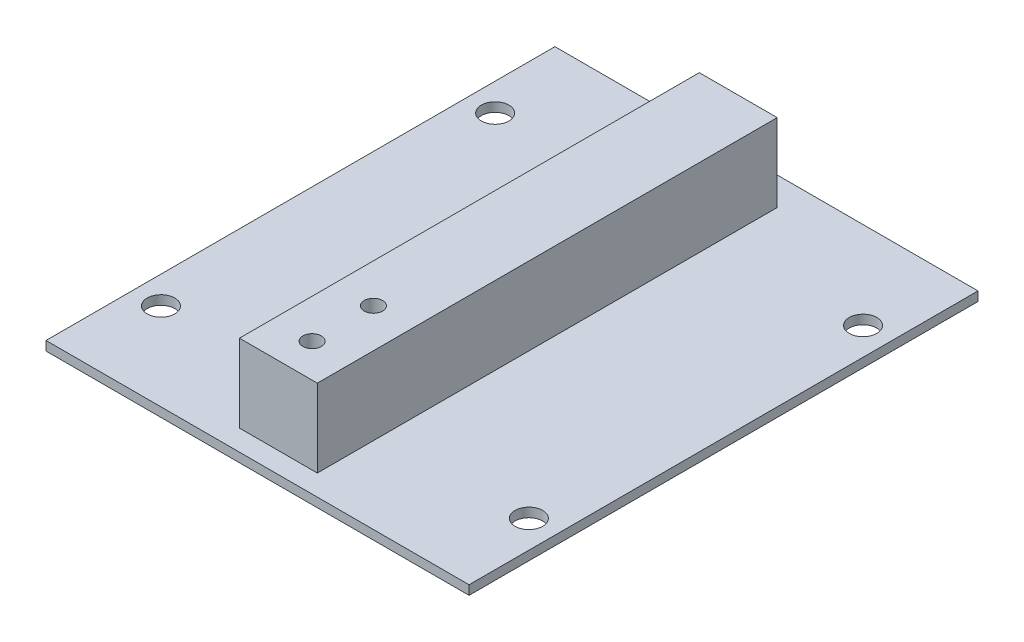
SolidWorks part; units mm, degrees
ref_plane "Front Plane" through (0, 0, 0) normal (0, 0, 1) x (1, 0, 0)
ref_plane "Top Plane" through (0, 0, 0) normal (0, 1, 0) x (1, 0, 0)
ref_plane "Right Plane" through (0, 0, 0) normal (1, 0, 0) x (0, 0, -1)
sketch "Sketch1" plane through (0, 0, 0) normal (0, 1, 0) x (1, 0, 0)
  line L1 (0, 0) -> (69, 0)
  line L2 (0, 0) -> (0, 83)
  line L3 (0, 83) -> (69, 83)
  line L4 (69, 0) -> (69, 83)
  line L5 (4.5, 14.25) -> (64.5, 14.25) construction
  line L6 (4.5, 14.25) -> (4.5, 68.75) construction
  line L7 (4.5, 68.75) -> (64.5, 68.75) construction
  line L8 (64.5, 14.25) -> (64.5, 68.75) construction
  circle A0 centre (4.5, 68.75) radius 2.25
  circle A1 centre (64.5, 68.75) radius 2.25
  circle A2 centre (64.5, 14.25) radius 2.25
  circle A3 centre (4.5, 14.25) radius 2.25
  point P5 (34.5, 68.75)
  point P18 (34.5, 83)
  point P19 (4.5, 41.5)
  point P20 (0, 41.5)
  dimension "D3" = 4.5
  dimension "D4" = 60
  dimension "D1" = 69
  dimension "D2" = 83
  dimension "5" = 50
extrude "Boss-Extrude1" add sketch "Sketch1" along normal blind 1.5
sketch "Sketch2" plane through (0, 1.5, 0) normal (0, 1, 0) x (1, 0, 0)
  line L0 (69, 83) -> (0, 83) construction
  line L1 (28.15, 3.4) -> (40.85, 3.4)
  line L2 (28.15, 3.4) -> (28.15, 78.4)
  line L3 (28.15, 78.4) -> (40.85, 78.4)
  line L4 (40.85, 3.4) -> (40.85, 78.4)
  circle A0 centre (34.5, 8.9) radius 1.5
  circle A1 centre (34.5, 18.9) radius 1.5
  point P6 (34.5, 83)
  point P7 (34.5, 78.4)
  dimension "D4" = 5.5
  dimension "3mm" = 3
  dimension "D1" = 12.7
  dimension "D2" = 75
  dimension "D3" = 4.6
  dimension "D5" = 10
extrude "Boss-Extrude2" add sketch "Sketch2" along normal blind 12.7
